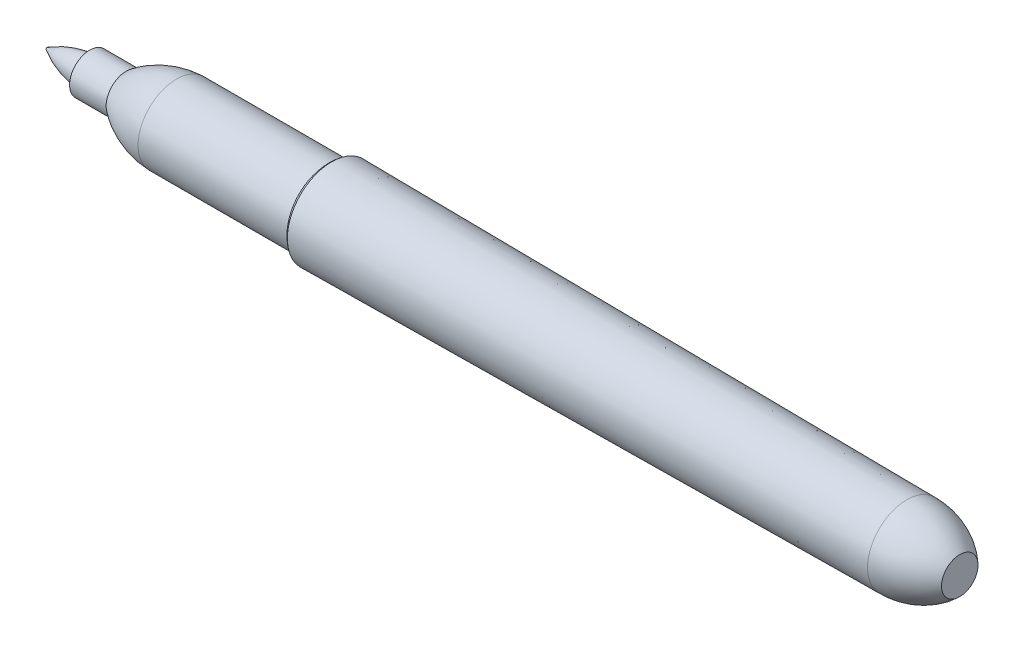
SolidWorks part; units mm, degrees
other "Camera1"
ref_plane "Front Plane" through (0, 0, 0) normal (0, 0, 1) x (1, 0, 0)
ref_plane "Top Plane" through (0, 0, 0) normal (0, 1, 0) x (1, 0, 0)
ref_plane "Right Plane" through (0, 0, 0) normal (1, 0, 0) x (0, 0, -1)
sketch "Sketch9" plane through (0, 0, 0) normal (0, 0, 1) x (1, 0, 0)
  line L0 (0, 0) -> (-127, 0) construction
  line L1 (0, 0) -> (0, 2.54)
  line L2 (-7.366, 0) -> (-7.366, 5.461)
  line L3 (-87.376, 0) -> (-87.376, 6.1595)
  line L4 (-88.138, 0) -> (-88.138, 5.334)
  line L5 (-108.966, 0) -> (-108.966, 5.334)
  line L6 (-115.951, 0) -> (-115.951, 2.794)
  line L7 (-127, 0.127) -> (-127, 0)
  line L8 (-121.031, 0) -> (-121.031, 1.905)
  line L10 (-121.031, 0) -> (-121.031, 2.794)
  line L11 (-121.031, 2.794) -> (-115.951, 2.794)
  line L12 (-108.966, 5.334) -> (-88.138, 5.334)
  line L13 (-87.376, 6.1595) -> (-7.366, 5.461)
  arc A0 (-127, 0.127) -> (-121.031, 1.905) centre (-120.4693, -10.8891) cw
  arc A1 (-88.138, 5.334) -> (-87.376, 6.1595) centre (-85.9453, 4.0744) cw
  arc A2 (-7.366, 5.461) -> (0, 2.54) centre (-7.2647, -5.0315) cw
  arc A3 (-115.951, 2.794) -> (-108.966, 5.334) centre (-108.4663, -6.9145) cw
  point P6 (0, 0)
  point P9 (-7.366, 0)
  point P12 (-87.376, 0)
  point P15 (-88.138, 0)
  point P18 (-108.966, 0)
  point P21 (-115.951, 0)
  point P24 (-121.031, 0)
  point P27 (-121.031, 0)
  point P30 (-127, 0)
  dimension "D1" = 127
  dimension "D4" = 7.366
  dimension "D6" = 80.01
  dimension "D8" = 88.138
  dimension "D10" = 20.828
revolve "Revolve2" add sketch "Sketch9" angle 360 about L0
fillet "Fillet1" radius 0.127 1 edges at (-127, 0.127, 0)
